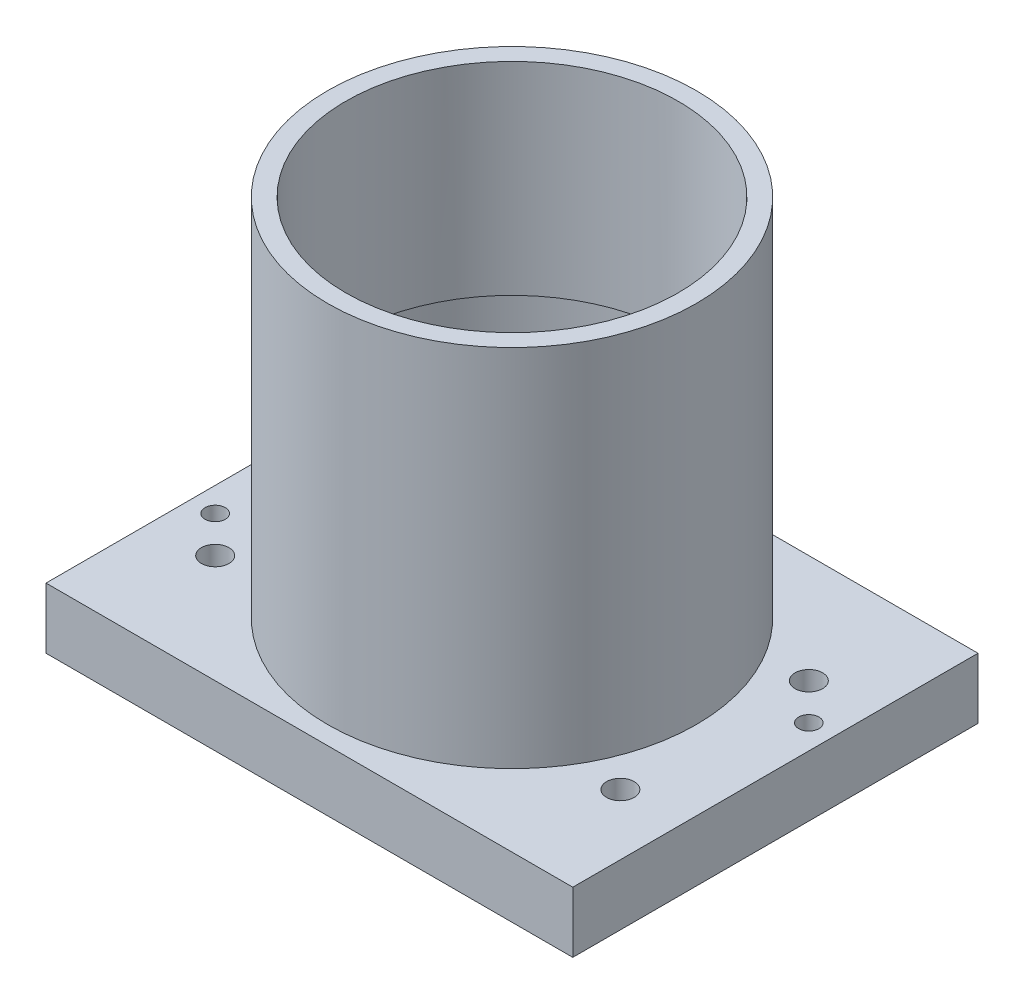
SolidWorks part; units mm, degrees
material "3003 Alloy"
ref_plane "Front Plane" through (0, 0, 0) normal (0, 0, 1) x (1, 0, 0)
ref_plane "Top Plane" through (0, 0, 0) normal (0, 1, 0) x (1, 0, 0)
ref_plane "Right Plane" through (0, 0, 0) normal (1, 0, 0) x (0, 0, -1)
sketch "Sketch1" plane through (0, 0, 0) normal (0, 1, 0) x (1, 0, 0)
  line L1 (-65, -50) -> (65, -50)
  line L2 (-65, -50) -> (-65, 50)
  line L3 (-65, 50) -> (65, 50)
  line L4 (65, -50) -> (65, 50)
  line L5 (-65, -50) -> (65, 50) construction
  line L6 (-65, 50) -> (65, -50) construction
  point P0 (0, 0)
  dimension "D1" = 130
  dimension "D2" = 100
extrude "Boss-Extrude1" add sketch "Sketch1" along normal blind 15
sketch "Sketch2" plane through (0, 15, 0) normal (0, 1, 0) x (1, 0, 0)
  circle A0 centre (0, 0) radius 45.5
  dimension "D1" = 91
extrude "Boss-Extrude2" add sketch "Sketch2" along normal blind 90
sketch "Sketch3" plane through (0, 105, 0) normal (0, 1, 0) x (1, 0, 0)
  circle A0 centre (0, 0) radius 41
  dimension "D1" = 82
extrude "Cut-Extrude1" cut sketch "Sketch3" against normal through all
sketch "Sketch4" plane through (0, 0, 0) normal (0, -1, 0) x (1, 0, 0)
  circle A0 centre (0, 0) radius 42.5
  dimension "D1" = 85
extrude "Cut-Extrude2" cut sketch "Sketch4" against normal blind 55
sketch "Sketch8" plane through (0, 15, 0) normal (0, 1, 0) x (1, 0, 0)
  line L0 (-50, 23.25) -> (50, 23.25) construction
  line L1 (50, 23.25) -> (50, -23.25) construction
  point P0 (-50, 23.25)
  point P1 (-50, -23.25)
  point P2 (50, 23.25)
  point P3 (50, -23.25)
  point P9 (0, 23.25)
  point P11 (50, 0)
  dimension "D1" = 100
  dimension "D2" = 46.5
hole_wizard "M8 Tapped Hole1" positions "Sketch9" profile "Sketch10" tap size "M8" standard "ISO"
sketch "Sketch9" plane through (0, 15, 0) normal (0, 1, 0) x (1, 0, 0)
  point P0 (-50, 23.25)
  point P3 (-50, -23.25)
  point P6 (50, -23.25)
  point P9 (50, 23.25)
sketch "Sketch10" plane through (-50, 15, -23.25) normal (1, 0, 0) x (0, 0, 1)
  line L0 (0, 0) -> (0, 19.75)
  line L1 (0, 19.75) -> (3.4, 17.7071)
  line L2 (3.4, 17.7071) -> (3.4, 0)
  line L5 (3.4, 0) -> (0, 0)
  line L10 (0, 19.75) -> (-3.4, 17.7071) construction
  line L11 (0, -6.35) -> (0, 107.95) construction
  dimension "Tap Drill Dia." = 6.8
  dimension "Tap Drill Depth" = 19.75
  dimension "Drill Angle" = 118
cosmetic thread "Hole Thread1" parameters "D1"=16, "D2"=8
cosmetic thread "Hole Thread2" parameters "D1"=16, "D2"=8
cosmetic thread "Hole Thread3" parameters "D1"=16, "D2"=8
cosmetic thread "Hole Thread4" parameters "D1"=16, "D2"=8
sketch "Sketch11" plane through (0, 0, 0) normal (0, -1, 0) x (1, 0, 0)
  circle A0 centre (-59, 14.25) radius 2.5
  circle A1 centre (59, -14.25) radius 2.5
  circle A2 centre (-50, 23.25) radius 3.4 construction
  circle A3 centre (50, -23.25) radius 3.4 construction
  dimension "D1" = 5
  dimension "D2" = 9
  dimension "D3" = 9
  dimension "D4" = 9
  dimension "D5" = 9
extrude "Cut-Extrude3" cut sketch "Sketch11" against normal through all
